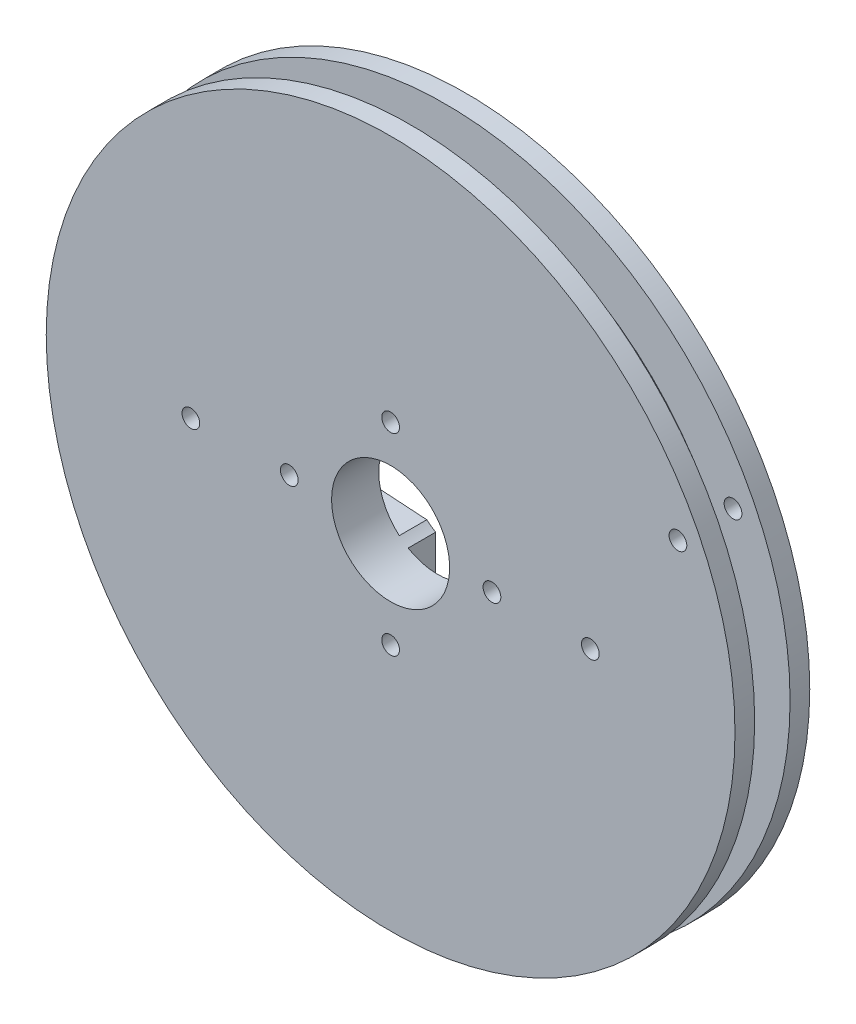
SolidWorks part; units mm, degrees
ref_plane "Front Plane" through (0, 0, 0) normal (0, 0, 1) x (1, 0, 0)
ref_plane "Top Plane" through (0, 0, 0) normal (0, 1, 0) x (1, 0, 0)
ref_plane "Right Plane" through (0, 0, 0) normal (1, 0, 0) x (0, 0, -1)
sketch "Sketch1" plane through (0, 0, 0) normal (0, 0, 1) x (1, 0, 0)
  circle A0 centre (0, 0) radius 19.05
  dimension "D1" = 38.1
extrude "Boss-Extrude1" add sketch "Sketch1" along normal mid plane 2.286
sketch "Sketch2" plane through (0, 0, 1.143) normal (0, 0, 1) x (1, 0, 0)
  circle A0 centre (0, 0) radius 22.225
  dimension "D1" = 44.45
extrude "Boss-Extrude2" add sketch "Sketch2" along normal blind 1.27
mirror "Mirror1" about plane through (0, 0, 0) normal (0, 0, 1) of "Boss-Extrude2"
sketch "Sketch3" plane through (0, 0, -2.413) normal (0, 0, -1) x (-1, 0, 0)
  circle A0 centre (0, 0) radius 3.556
  dimension "D1" = 7.112
extrude "Cut-Extrude1" cut sketch "Sketch3" against normal through all
sketch "Sketch4" plane through (0, 0, -2.413) normal (0, 0, -1) x (-1, 0, 0)
  line L0 (-19.05, 0) -> (19.05, 0) construction
  line L1 (13.462, 0.6572) -> (13.462, -0.8511) construction
  line L2 (0, 0) -> (0, 17.8222) construction
  circle A0 centre (0, 0) radius 19.05 construction
  circle A1 centre (0, 0) radius 19.05 construction
  circle A2 centre (12.8905, 0) radius 0.5715
  circle A3 centre (6.5405, 0) radius 0.5715
  circle A4 centre (-12.8905, 0) radius 0.5715
  circle A5 centre (-6.5405, 0) radius 0.5715
  point P8 (0, 0)
  dimension "D2" = 1.143
  dimension "D1" = 6.35
  dimension "D3" = 5.588
extrude "Cut-Extrude3" cut sketch "Sketch4" against normal through all
sketch "Sketch5" plane through (0, 0, -2.413) normal (0, 0, -1) x (-1, 0, 0)
  circle A0 centre (-18.542, 8.89) radius 0.5715
  circle A1 centre (0, 0) radius 19.05 construction
  circle A2 centre (0, 0) radius 19.05 construction
  circle A3 centre (-12.8905, 0) radius 0.5715 construction
  dimension "D1" = 8.89
  dimension "D2" = 18.542
extrude "Cut-Extrude4" cut sketch "Sketch5" against normal through all
sketch "Sketch6" plane through (0, 0, -2.413) normal (0, 0, -1) x (-1, 0, 0)
  line L0 (0, 0) -> (-14.9263, 17.3101) construction
  line L1 (0, 0) -> (15.9208, 19.5006) construction
  line L2 (0, 0) -> (-27.4134, -0.3688) construction
  line L3 (0, 0) -> (-17.6766, -21.6511) construction
  line L4 (0, 0) -> (16.2688, -18.867) construction
  line L5 (0, 0) -> (21.6822, 8.2237) construction
  line L6 (0, 0) -> (21.0847, -7.3545) construction
  line L13 (-13.5185, 15.6774) -> (-14.5137, 16.8316)
  line L14 (13.0918, 16.0355) -> (14.0556, 17.216)
  line L15 (19.3556, 7.3412) -> (20.7805, 7.8817)
  line L16 (19.5461, -6.8178) -> (20.985, -7.3197)
  line L17 (-14.0556, -17.216) -> (-13.0918, -16.0355)
  line L18 (13.5185, -15.6774) -> (14.5137, -16.8316)
  circle A1 centre (0, 0) radius 22.225 construction
  arc A3 (-14.0556, -17.216) -> (14.5137, -16.8316) centre (0, 0) ccw
  arc A4 (14.0556, 17.216) -> (-14.5137, 16.8316) centre (0, 0) ccw
  arc A6 (20.985, -7.3197) -> (20.7805, 7.8817) centre (0, 0) ccw
  arc A8 (-13.5185, 15.6774) -> (13.0918, 16.0355) centre (0, 0) cw
  arc A9 (19.3556, 7.3412) -> (19.5461, -6.8178) centre (0, 0) cw
  arc A10 (-13.0918, -16.0355) -> (13.5185, -15.6774) centre (0, 0) ccw
  dimension "D5" = 1.524
  dimension "D6" = 1.524
  dimension "D7" = 1.524
  dimension "D1" = 80
  dimension "D2" = 50
  dimension "D3" = 30
  dimension "D4" = 30
sketch "Sketch7" plane through (0, 0, -2.413) normal (0, 0, -1) x (-1, 0, 0)
  line L0 (0, -8.3693) -> (0, 8.3693) construction
  line L2 (0, 0) -> (31.6779, 0) construction
  line L3 (-6.103, 2.921) -> (8.4265, 2.921) construction
  line L4 (-6.103, -3.048) -> (7.7443, -3.048) construction
  line L5 (-1.9177, 3.6195) -> (-1.9177, 6.4262)
  line L6 (1.9177, 2.921) -> (1.9177, 6.4262)
  line L7 (-1.9177, 4.6736) -> (1.9177, 4.6736) construction
  line L8 (-16.9028, 2.0955) -> (-1.9177, 3.6195)
  line L9 (14.6728, 2.0955) -> (1.9177, 2.921)
  line L10 (14.6728, -2.0955) -> (1.9177, -2.921)
  line L11 (1.9177, -2.921) -> (1.9177, -6.4262)
  line L12 (-1.9177, -3.6195) -> (-1.9177, -6.4262)
  line L13 (-16.9028, -2.0955) -> (-1.9177, -3.6195)
  arc A0 (-1.9177, 6.4262) -> (1.9177, 6.4262) centre (0, 6.4262) cw
  arc A1 (-16.9028, -2.0955) -> (-16.9028, 2.0955) centre (-16.6897, 0) cw
  arc A2 (14.6728, -2.0955) -> (14.6728, 2.0955) centre (14.2441, 0) ccw
  arc A3 (-1.9177, -6.4262) -> (1.9177, -6.4262) centre (0, -6.4262) ccw
  point P3 (-18.796, 0)
  point P4 (0, 8.3439)
  point P8 (0, 0)
  point P18 (0, 4.6736)
  point P38 (16.383, 0)
  point P39 (0, -8.3439)
  dimension "D7" = 16.383
  dimension "D10" = 4.191
  dimension "D1" = 7.239
  dimension "D2" = 16.7386
  dimension "D3" = 5.969
  dimension "D4" = 2.921
  dimension "D5" = 3.8354
  dimension "D6" = 3.5052
  dimension "D8" = 4.191
  dimension "D9" = 18.796
  dimension "D11" = 12.7551
extrude "Cut-Extrude5" cut sketch "Sketch7" against normal blind 1.778
sketch "Sketch10" plane through (0, 0, -2.413) normal (0, 0, -1) x (-1, 0, 0)
  line L0 (-22.225, 0) -> (22.225, 0) construction
  line L1 (0, -22.225) -> (0, 22.225) construction
  circle A0 centre (0, 0) radius 22.225 construction
  circle A2 centre (0, -6.223) radius 0.5715
  circle A3 centre (0, 6.223) radius 0.5715
  circle A4 centre (-6.5405, 0) radius 0.5715 construction
  point P8 (0, 0)
  point P14 (0, 0)
  dimension "D1" = 6.223
  dimension "D2" = 6.223
extrude "Cut-Extrude6" cut sketch "Sketch10" against normal through all
sketch "Sketch11" plane through (0, 0, -2.413) normal (0, 0, -1) x (-1, 0, 0)
  circle A0 centre (0, 0) radius 3.81
  dimension "D1" = 7.62
extrude "Cut-Extrude7" cut sketch "Sketch11" against normal through all
